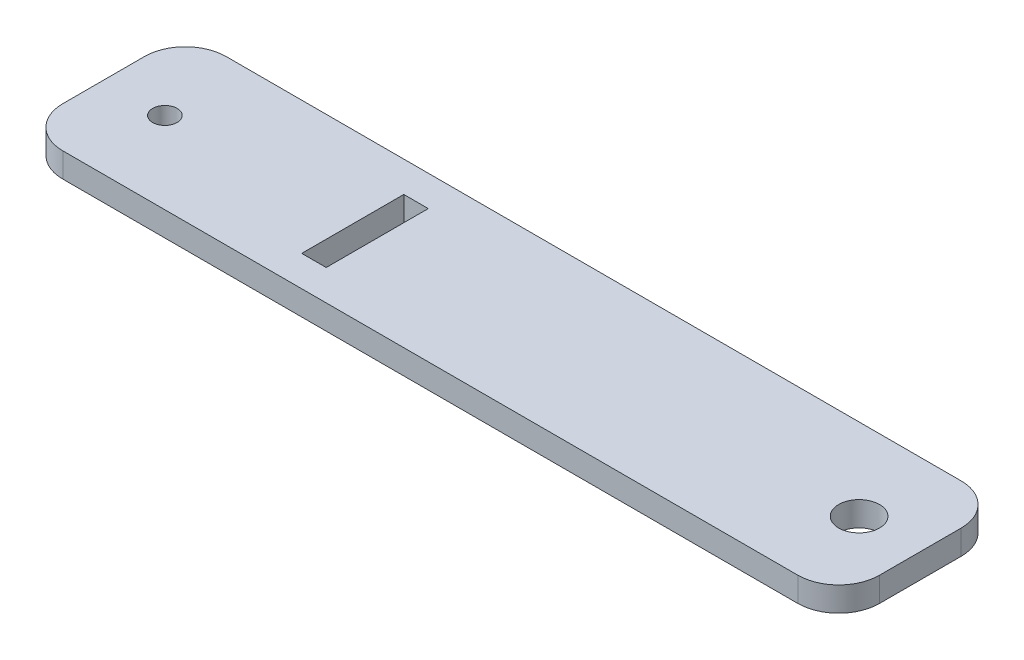
SolidWorks part; units mm, degrees
ref_plane "Front Plane" through (0, 0, 0) normal (0, 0, 1) x (1, 0, 0)
ref_plane "Top Plane" through (0, 0, 0) normal (0, 1, 0) x (1, 0, 0)
ref_plane "Right Plane" through (0, 0, 0) normal (1, 0, 0) x (0, 0, -1)
sketch "Sketch2" plane through (0, 0, 0) normal (0, 1, 0) x (1, 0, 0)
  line L0 (100, 0) -> (85, 0) construction
  line L1 (-90, 20) -> (90, 20)
  line L2 (-100, 10) -> (-100, -10)
  line L3 (-90, -20) -> (90, -20)
  line L4 (100, 10) -> (100, -10)
  line L5 (-100, 20) -> (100, -20) construction
  line L6 (-100, -20) -> (100, 20) construction
  line L7 (-100, 0) -> (-85, 0) construction
  line L8 (-85, 0) -> (-39, 0) construction
  line L9 (-39, 0) -> (-36, 0) construction
  line L11 (-39, 12.5) -> (-33, 12.5)
  line L12 (-39, 12.5) -> (-39, -12.5)
  line L13 (-39, -12.5) -> (-33, -12.5)
  line L14 (-33, 12.5) -> (-33, -12.5)
  line L15 (-39, 12.5) -> (-33, -12.5) construction
  line L16 (-39, -12.5) -> (-33, 12.5) construction
  arc A0 (90, -20) -> (100, -10) centre (90, -10) ccw
  arc A1 (90, 20) -> (100, 10) centre (90, 10) cw
  arc A2 (-100, -10) -> (-90, -20) centre (-90, -10) ccw
  arc A3 (-90, 20) -> (-100, 10) centre (-90, 10) ccw
  circle A4 centre (85, 0) radius 5
  circle A5 centre (-85, 0) radius 3
  point P0 (0, 0)
  dimension "D1" = 10
  dimension "D2" = 40
  dimension "D3" = 200
extrude "Boss-Extrude1" add sketch "Sketch2" along normal blind 6
